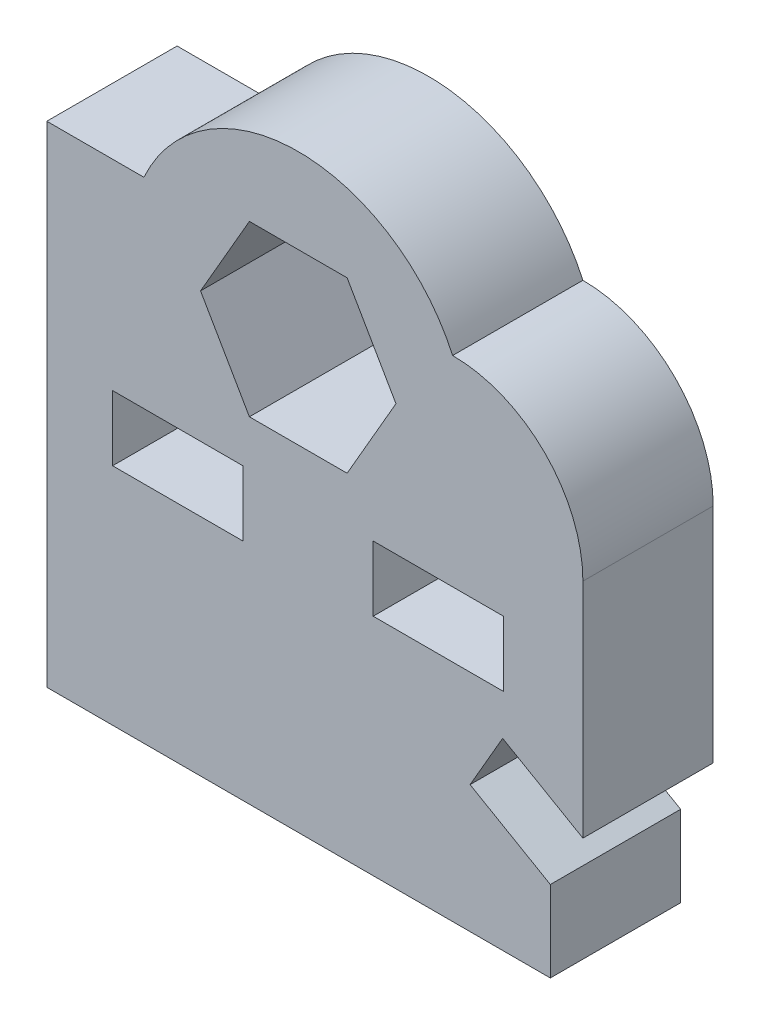
SolidWorks part; units mm, degrees
ref_plane "Front Plane" through (0, 0, 0) normal (0, 0, 1) x (1, 0, 0)
ref_plane "Top Plane" through (0, 0, 0) normal (0, 1, 0) x (1, 0, 0)
ref_plane "Right Plane" through (0, 0, 0) normal (1, 0, 0) x (0, 0, -1)
sketch "Sketch1" plane through (0, 0, 0) normal (0, 0, 1) x (1, 0, 0)
  line L0 (14.4756, 6) -> (15.4756, 7.7321)
  line L1 (3.5, 8.9911) -> (3.5, 10.9911)
  line L2 (16.9397, 2.0911) -> (1.48, 2.0911)
  line L3 (1.48, 17.1426) -> (1.48, 2.0911)
  line L4 (17.9397, 13.1426) -> (17.9397, 6.3094)
  line L5 (4.4603, 17.1426) -> (1.48, 17.1426)
  line L7 (16.9397, 4.5774) -> (16.9397, 2.0911)
  line L8 (7.5, 8.9911) -> (7.5, 10.9911)
  line L9 (3.5, 8.9911) -> (7.5, 8.9911)
  line L10 (15.4756, 7.7321) -> (17.9397, 6.3094)
  line L11 (3.5, 10.9911) -> (7.5, 10.9911)
  line L12 (14.4756, 6) -> (16.9397, 4.5774)
  line L13 (11.5, 8.9911) -> (11.5, 10.9911)
  line L14 (11.5, 8.9911) -> (15.5, 8.9911)
  line L15 (15.5, 8.9911) -> (15.5, 10.9911)
  line L16 (11.5, 10.9911) -> (15.5, 10.9911)
  line L20 (6.2, 14.9911) -> (7.7, 12.393)
  line L21 (7.7, 12.393) -> (10.7, 12.393)
  line L22 (10.7, 12.393) -> (12.2, 14.9911)
  line L23 (12.2, 14.9911) -> (10.7, 17.5892)
  line L24 (10.7, 17.5892) -> (7.7, 17.5892)
  line L25 (7.7, 17.5892) -> (6.2, 14.9911)
  arc A0 (17.9397, 13.1426) -> (13.9397, 17.1426) centre (13.9397, 13.1426) ccw
  arc A3 (13.9397, 17.1426) -> (4.4603, 17.1426) centre (9.2, 14.9926) ccw
  dimension "D1" = 4
  dimension "D9" = 7.7
  dimension "D6" = 4.4603
  dimension "D3" = 5.2045
  dimension "D5" = 3.5
  dimension "D7" = 6.2
  dimension "D10" = 9.2
  dimension "D11" = 10.7
  dimension "D13" = 11.5
  dimension "D14" = 14.4756
  dimension "D15" = 15.4756
  dimension "D18" = 4.5774
  dimension "D19" = 8.9911
  dimension "D20" = 12.393
  dimension "D21" = 14.9926
extrude "Boss-Extrude1" add sketch "Sketch1" along normal blind 4
